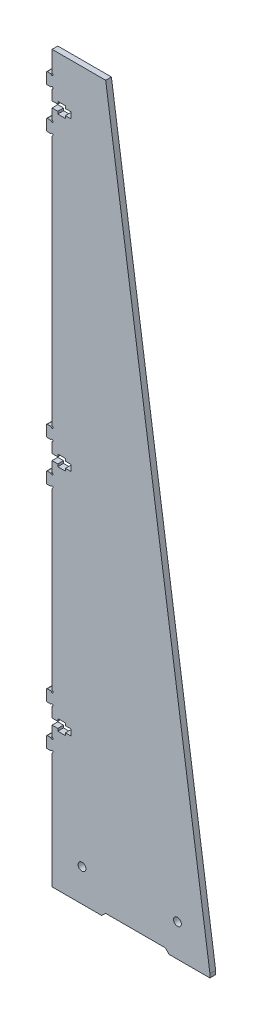
SolidWorks part; units mm, degrees
ref_plane "Alzado" through (0, 0, 0) normal (0, 0, 1) x (1, 0, 0)
ref_plane "Planta" through (0, 0, 0) normal (0, 1, 0) x (1, 0, 0)
ref_plane "Vista lateral" through (0, 0, 0) normal (1, 0, 0) x (0, 0, -1)
sketch "Model" plane through (0, 0, 0) normal (0, 0, 1) x (1, 0, 0)
  line L0 (458.6581, 643.9963) -> (476.091, 643.9963)
  line L1 (458.6581, 643.9963) -> (448.0081, 643.9963)
  line L2 (448.0081, 643.9963) -> (448.0081, 633.4623)
  line L3 (447.1421, 632.5963) -> (445.508, 632.5963)
  line L4 (445.008, 632.0963) -> (445.008, 627.0963)
  line L5 (445.508, 626.5963) -> (447.1421, 626.5963)
  line L6 (448.0081, 625.7303) -> (448.0081, 620.5963)
  line L7 (448.0081, 620.5963) -> (451.0081, 620.5963)
  line L8 (451.0081, 620.5963) -> (451.0081, 621.8713)
  line L9 (451.0081, 621.8713) -> (455.0081, 621.8713)
  line L10 (455.0081, 621.8713) -> (455.0081, 620.5963)
  line L11 (455.0081, 620.5963) -> (458.0081, 620.5963)
  line L12 (458.0081, 620.5963) -> (458.0081, 617.3963)
  line L13 (458.0081, 617.3963) -> (455.0081, 617.3963)
  line L14 (455.0081, 617.3963) -> (455.0081, 616.1213)
  line L15 (455.0081, 616.1213) -> (451.0081, 616.1213)
  line L16 (451.0081, 616.1213) -> (451.0081, 617.3963)
  line L17 (451.0081, 617.3963) -> (448.0081, 617.3963)
  line L18 (448.0081, 617.3963) -> (448.0081, 612.2623)
  line L19 (447.1421, 611.3963) -> (445.508, 611.3963)
  line L20 (445.008, 610.8963) -> (445.008, 605.8963)
  line L21 (445.508, 605.3963) -> (447.1421, 605.3963)
  line L22 (448.0081, 604.5303) -> (448.0081, 473.4641)
  line L23 (448.0081, 473.4641) -> (448.0081, 473.4623)
  line L24 (447.1421, 472.5963) -> (445.508, 472.5963)
  line L25 (445.008, 472.0963) -> (445.008, 467.0963)
  line L26 (445.508, 466.5963) -> (447.1421, 466.5963)
  line L27 (448.0081, 465.7303) -> (448.0081, 460.5963)
  line L28 (448.0081, 460.5963) -> (451.0081, 460.5963)
  line L29 (451.0081, 460.5963) -> (451.0081, 461.8713)
  line L30 (451.0081, 461.8713) -> (455.0081, 461.8713)
  line L31 (455.0081, 461.8713) -> (455.0081, 460.5963)
  line L32 (455.0081, 460.5963) -> (458.0081, 460.5963)
  line L33 (458.0081, 460.5963) -> (458.0081, 457.3963)
  line L34 (458.0081, 457.3963) -> (455.0081, 457.3963)
  line L35 (455.0081, 457.3963) -> (455.0081, 456.1213)
  line L36 (455.0081, 456.1213) -> (451.0081, 456.1213)
  line L37 (451.0081, 456.1213) -> (451.0081, 457.3963)
  line L38 (451.0081, 457.3963) -> (448.0081, 457.3963)
  line L39 (448.0081, 457.3963) -> (448.0081, 452.2623)
  line L40 (447.1421, 451.3963) -> (445.508, 451.3963)
  line L41 (445.008, 450.8963) -> (445.008, 445.8963)
  line L42 (445.508, 445.3963) -> (447.1421, 445.3963)
  line L43 (448.0081, 444.5303) -> (448.0081, 353.4641)
  line L44 (448.0081, 353.4641) -> (448.0081, 353.4623)
  line L45 (447.1421, 352.5963) -> (445.508, 352.5963)
  line L46 (445.008, 352.0963) -> (445.008, 347.0963)
  line L47 (445.508, 346.5963) -> (447.1421, 346.5963)
  line L48 (448.0081, 345.7303) -> (448.0081, 340.5963)
  line L49 (448.0081, 340.5963) -> (451.0081, 340.5963)
  line L50 (451.0081, 340.5963) -> (451.0081, 341.8713)
  line L51 (451.0081, 341.8713) -> (455.0081, 341.8713)
  line L52 (455.0081, 341.8713) -> (455.0081, 340.5963)
  line L53 (455.0081, 340.5963) -> (458.0081, 340.5963)
  line L54 (458.0081, 340.5963) -> (458.0081, 337.3963)
  line L55 (458.0081, 337.3963) -> (455.0081, 337.3963)
  line L56 (455.0081, 337.3963) -> (455.0081, 336.1213)
  line L57 (455.0081, 336.1213) -> (451.0081, 336.1213)
  line L58 (451.0081, 336.1213) -> (451.0081, 337.3963)
  line L59 (451.0081, 337.3963) -> (448.0081, 337.3963)
  line L60 (448.0081, 337.3963) -> (448.0081, 332.2623)
  line L61 (447.1421, 331.3963) -> (445.508, 331.3963)
  line L62 (445.008, 330.8963) -> (445.008, 325.8963)
  line L63 (445.508, 325.3963) -> (447.1421, 325.3963)
  line L64 (476.091, 643.9963) -> (524.4971, 308.953)
  line L65 (524.4971, 308.953) -> (530.7033, 265.9963)
  line L66 (448.0081, 324.5303) -> (448.0081, 263.9963)
  line L67 (448.0081, 263.9963) -> (474.0081, 263.9963)
  line L68 (474.0081, 263.9963) -> (476.0081, 265.9963)
  line L69 (476.0081, 265.9963) -> (507.3283, 265.9963)
  line L70 (507.3283, 265.9963) -> (509.3283, 263.9963)
  line L71 (509.3283, 263.9963) -> (530.7033, 263.9963)
  line L72 (530.7033, 265.9963) -> (530.7033, 263.9963)
  arc A0 (448.0081, 633.4623) -> (448.2581, 633.0293) centre (448.5081, 633.4623) ccw
  arc A1 (447.5751, 632.3463) -> (448.2581, 633.0293) centre (448.0081, 632.5963) ccw
  arc A2 (447.5751, 632.3463) -> (447.1421, 632.5963) centre (447.1421, 632.0963) ccw
  arc A3 (445.508, 632.5963) -> (445.008, 632.0963) centre (445.508, 632.0963) ccw
  arc A4 (445.008, 627.0963) -> (445.508, 626.5963) centre (445.508, 627.0963) ccw
  arc A5 (447.1421, 626.5963) -> (447.5751, 626.8463) centre (447.1421, 627.0963) ccw
  arc A6 (448.2581, 626.1633) -> (447.5751, 626.8463) centre (448.0081, 626.5963) ccw
  arc A7 (448.2581, 626.1633) -> (448.0081, 625.7303) centre (448.5081, 625.7303) ccw
  arc A8 (448.0081, 612.2623) -> (448.2581, 611.8293) centre (448.5081, 612.2623) ccw
  arc A9 (447.5751, 611.1463) -> (448.2581, 611.8293) centre (448.0081, 611.3963) ccw
  arc A10 (447.5751, 611.1463) -> (447.1421, 611.3963) centre (447.1421, 610.8963) ccw
  arc A11 (445.508, 611.3963) -> (445.008, 610.8963) centre (445.508, 610.8963) ccw
  arc A12 (445.008, 605.8963) -> (445.508, 605.3963) centre (445.508, 605.8963) ccw
  arc A13 (447.1421, 605.3963) -> (447.5751, 605.6463) centre (447.1421, 605.8963) ccw
  arc A14 (448.2581, 604.9633) -> (447.5751, 605.6463) centre (448.0081, 605.3963) ccw
  arc A15 (448.2581, 604.9633) -> (448.0081, 604.5303) centre (448.5081, 604.5303) ccw
  arc A16 (448.0081, 473.4623) -> (448.2581, 473.0293) centre (448.5081, 473.4623) ccw
  arc A17 (447.5751, 472.3463) -> (448.2581, 473.0293) centre (448.0081, 472.5963) ccw
  arc A18 (447.5751, 472.3463) -> (447.1421, 472.5963) centre (447.1421, 472.0963) ccw
  arc A19 (445.508, 472.5963) -> (445.008, 472.0963) centre (445.508, 472.0963) ccw
  arc A20 (445.008, 467.0963) -> (445.508, 466.5963) centre (445.508, 467.0963) ccw
  arc A21 (447.1421, 466.5963) -> (447.5751, 466.8463) centre (447.1421, 467.0963) ccw
  arc A22 (448.2581, 466.1633) -> (447.5751, 466.8463) centre (448.0081, 466.5963) ccw
  arc A23 (448.2581, 466.1633) -> (448.0081, 465.7303) centre (448.5081, 465.7303) ccw
  arc A24 (448.0081, 452.2623) -> (448.2581, 451.8293) centre (448.5081, 452.2623) ccw
  arc A25 (447.5751, 451.1463) -> (448.2581, 451.8293) centre (448.0081, 451.3963) ccw
  arc A26 (447.5751, 451.1463) -> (447.1421, 451.3963) centre (447.1421, 450.8963) ccw
  arc A27 (445.508, 451.3963) -> (445.008, 450.8963) centre (445.508, 450.8963) ccw
  arc A28 (445.008, 445.8963) -> (445.508, 445.3963) centre (445.508, 445.8963) ccw
  arc A29 (447.1421, 445.3963) -> (447.5751, 445.6463) centre (447.1421, 445.8963) ccw
  arc A30 (448.2581, 444.9633) -> (447.5751, 445.6463) centre (448.0081, 445.3963) ccw
  arc A31 (448.2581, 444.9633) -> (448.0081, 444.5303) centre (448.5081, 444.5303) ccw
  arc A32 (448.0081, 353.4623) -> (448.2581, 353.0293) centre (448.5081, 353.4623) ccw
  arc A33 (447.5751, 352.3463) -> (448.2581, 353.0293) centre (448.0081, 352.5963) ccw
  arc A34 (447.5751, 352.3463) -> (447.1421, 352.5963) centre (447.1421, 352.0963) ccw
  arc A35 (445.508, 352.5963) -> (445.008, 352.0963) centre (445.508, 352.0963) ccw
  arc A36 (445.008, 347.0963) -> (445.508, 346.5963) centre (445.508, 347.0963) ccw
  arc A37 (447.1421, 346.5963) -> (447.5751, 346.8463) centre (447.1421, 347.0963) ccw
  arc A38 (448.2581, 346.1633) -> (447.5751, 346.8463) centre (448.0081, 346.5963) ccw
  arc A39 (448.2581, 346.1633) -> (448.0081, 345.7303) centre (448.5081, 345.7303) ccw
  arc A40 (448.0081, 332.2623) -> (448.2581, 331.8293) centre (448.5081, 332.2623) ccw
  arc A41 (447.5751, 331.1463) -> (448.2581, 331.8293) centre (448.0081, 331.3963) ccw
  arc A42 (447.5751, 331.1463) -> (447.1421, 331.3963) centre (447.1421, 330.8963) ccw
  arc A43 (445.508, 331.3963) -> (445.008, 330.8963) centre (445.508, 330.8963) ccw
  arc A44 (445.008, 325.8963) -> (445.508, 325.3963) centre (445.508, 325.8963) ccw
  arc A45 (447.1421, 325.3963) -> (447.5751, 325.6463) centre (447.1421, 325.8963) ccw
  arc A46 (448.2581, 324.9633) -> (447.5751, 325.6463) centre (448.0081, 325.3963) ccw
  circle A47 centre (463.688, 280.9963) radius 2.05
  arc A48 (448.2581, 324.9633) -> (448.0081, 324.5303) centre (448.5081, 324.5303) ccw
  circle A49 centre (513.688, 280.9963) radius 2.05
extrude "Saliente-Extruir1" add sketch "Model" along normal blind 3
